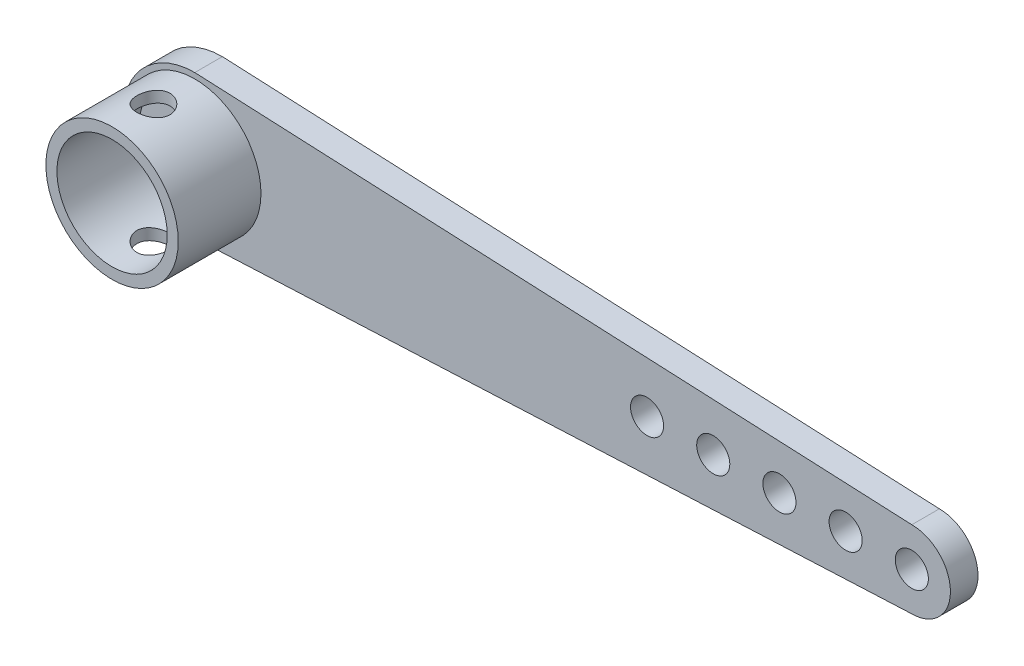
SolidWorks part; units mm, degrees
ref_plane "Płaszczyzna przednia" through (0, 0, 0) normal (0, 0, 1) x (1, 0, 0)
ref_plane "Płaszczyzna górna" through (0, 0, 0) normal (0, 1, 0) x (1, 0, 0)
ref_plane "Płaszczyzna prawa" through (0, 0, 0) normal (1, 0, 0) x (0, 0, -1)
sketch "Szkic2" plane through (0, 0, 0) normal (0, 0, 1) x (1, 0, 0)
  line L0 (0, 13) -> (130, 7)
  line L1 (0, -13) -> (130, -7)
  circle A0 centre (0, 0) radius 13
  circle A1 centre (130, 0) radius 7
  dimension "D1" = 26
  dimension "D2" = 14
  dimension "D3" = 130
extrude "Dodanie-wyciągnięcie1" add sketch "Szkic2" along normal blind 5 contours A1 L0 A0 L1 | A1 | L0 A0 L1
sketch "Szkic5" plane through (0, 0, 5) normal (0, 0, 1) x (1, 0, 0)
  circle A0 centre (0, 0) radius 12
  dimension "D1" = 24
extrude "Dodanie-wyciągnięcie3" add sketch "Szkic5" along normal blind 15
sketch "Szkic6" plane through (0, 0, 20) normal (0, 0, 1) x (1, 0, 0)
  circle A0 centre (0, 0) radius 10
  dimension "D1" = 20
extrude "Wytnij-wyciągnięcie1" cut sketch "Szkic6" against normal blind 15
sketch "Szkic7" plane through (0, 0, 0) normal (0, 1, 0) x (1, 0, 0)
  circle A0 centre (0, -12.5) radius 3
  dimension "D1" = 6
  dimension "D2" = 7.5
extrude "Wytnij-wyciągnięcie2" cut sketch "Szkic7" against normal mid plane 43
sketch "Szkic8" plane through (0, 0, 5) normal (0, 0, 1) x (1, 0, 0)
  circle A0 centre (130, 0) radius 3
  circle A1 centre (118, 0) radius 3
  circle A2 centre (106, 0) radius 3
  circle A3 centre (94, 0) radius 3
  circle A4 centre (82, 0) radius 3
  dimension "D1" = 6
  dimension "D2" = 6
  dimension "D3" = 6
  dimension "D4" = 6
  dimension "D5" = 6
  dimension "D6" = 12
  dimension "D7" = 12
  dimension "D8" = 12
  dimension "D9" = 12
extrude "Wytnij-wyciągnięcie3" cut sketch "Szkic8" against normal blind 43
